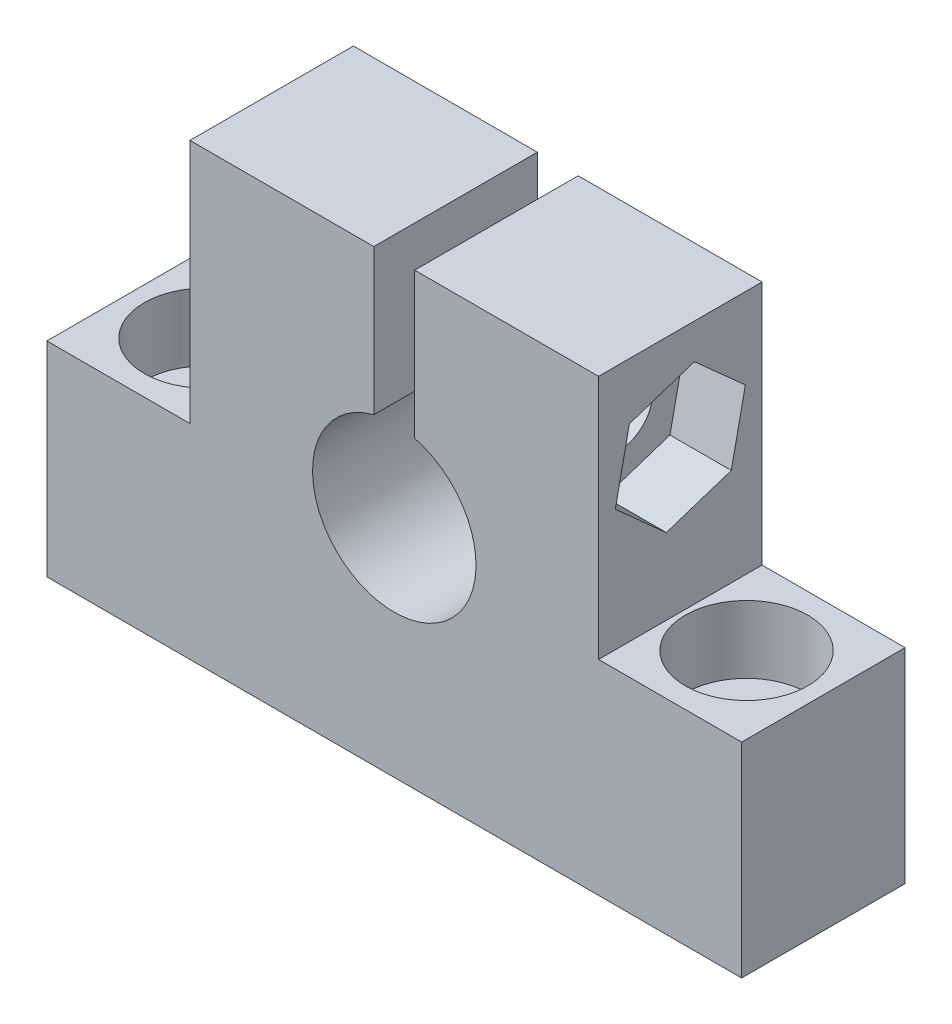
SolidWorks part; units mm, degrees
ref_plane "前视基准面" through (0, 0, 0) normal (0, 0, 1) x (1, 0, 0)
ref_plane "上视基准面" through (0, 0, 0) normal (0, 1, 0) x (1, 0, 0)
ref_plane "右视基准面" through (0, 0, 0) normal (1, 0, 0) x (0, 0, -1)
sketch "草图1" plane through (0, 0, 0) normal (0, 0, 1) x (1, 0, 0)
  line L0 (0, 0) -> (0, 30.4533) construction
  line L1 (-10, 22) -> (10, 22)
  line L2 (10, 22) -> (10, 10)
  line L3 (10, 10) -> (17, 10)
  line L4 (17, 10) -> (17, 0)
  line L5 (17, 0) -> (-17, 0)
  line L6 (-17, 10) -> (-17, 0)
  line L7 (-10, 10) -> (-17, 10)
  line L8 (-10, 22) -> (-10, 10)
  point P12 (0, 22)
  dimension "D1" = 20
  dimension "D2" = 34
  dimension "D3" = 10
  dimension "D4" = 22
extrude "凸台-拉伸1" add sketch "草图1" along normal blind 8
sketch "草图2" plane through (0, 0, 8) normal (0, 0, 1) x (1, 0, 0)
  line L0 (0, 0) -> (0, 41.462) construction
  line L1 (-17, 0) -> (17, 0) construction
  line L2 (-1, 22) -> (1, 22)
  line L3 (10, 22) -> (-10, 22) construction
  line L4 (1, 22) -> (1, 14.873)
  line L5 (-1, 22) -> (-1, 14.873)
  arc A0 (-1, 14.873) -> (1, 14.873) centre (0, 11) ccw
  point P14 (0, 22)
  dimension "D1" = 11
  dimension "D2" = 8
  dimension "D3" = 2
extrude "切除-拉伸1" cut sketch "草图2" against normal through all
sketch "草图3" plane through (-10, 0, 0) normal (-1, 0, 0) x (0, 0, 1)
  line L0 (4, 10) -> (4, 32.0252) construction
  line L1 (8, 10) -> (0, 10) construction
  line L2 (8, 0) -> (0, 0) construction
  circle A0 centre (4, 17) radius 1.65
  dimension "D1" = 3.3
  dimension "D2" = 17
extrude "切除-拉伸2" cut sketch "草图3" against normal through all
sketch "草图4" plane through (-10, 0, 0) normal (-1, 0, 0) x (0, 0, 1)
  circle A0 centre (4, 17) radius 3
  dimension "D1" = 6
extrude "切除-拉伸3" cut sketch "草图4" against normal blind 3.3
sketch "草图5" plane through (10, 0, 0) normal (1, 0, 0) x (0, 0, -1)
  line L1 (-6.4941, 19.2344) -> (-7.1821, 15.9573)
  line L2 (-7.1821, 15.9573) -> (-4.688, 13.7228)
  line L3 (-4.688, 13.7228) -> (-1.5059, 14.7656)
  line L4 (-1.5059, 14.7656) -> (-0.8179, 18.0427)
  line L5 (-0.8179, 18.0427) -> (-3.312, 20.2772)
  line L6 (-3.312, 20.2772) -> (-6.4941, 19.2344)
  circle A0 centre (-4, 17) radius 2.9 construction
  dimension "D1" = 5.8
extrude "切除-拉伸4" cut sketch "草图5" against normal blind 3
sketch "草图6" plane through (0, 10, 0) normal (0, 1, 0) x (1, 0, 0)
  line L1 (0, 0) -> (0, -13.9544) construction
  circle A0 centre (-13.2396, -4) radius 1.65
  circle A1 centre (13.2396, -4) radius 1.65
  dimension "D1" = 3.3
extrude "切除-拉伸5" cut sketch "草图6" against normal through all
sketch "草图7" plane through (0, 10, 0) normal (0, 1, 0) x (1, 0, 0)
  circle A0 centre (13.2396, -4) radius 3
  circle A1 centre (-13.2396, -4) radius 3
  dimension "D1" = 6
  dimension "D2" = 6
extrude "切除-拉伸6" cut sketch "草图7" against normal blind 3.3
